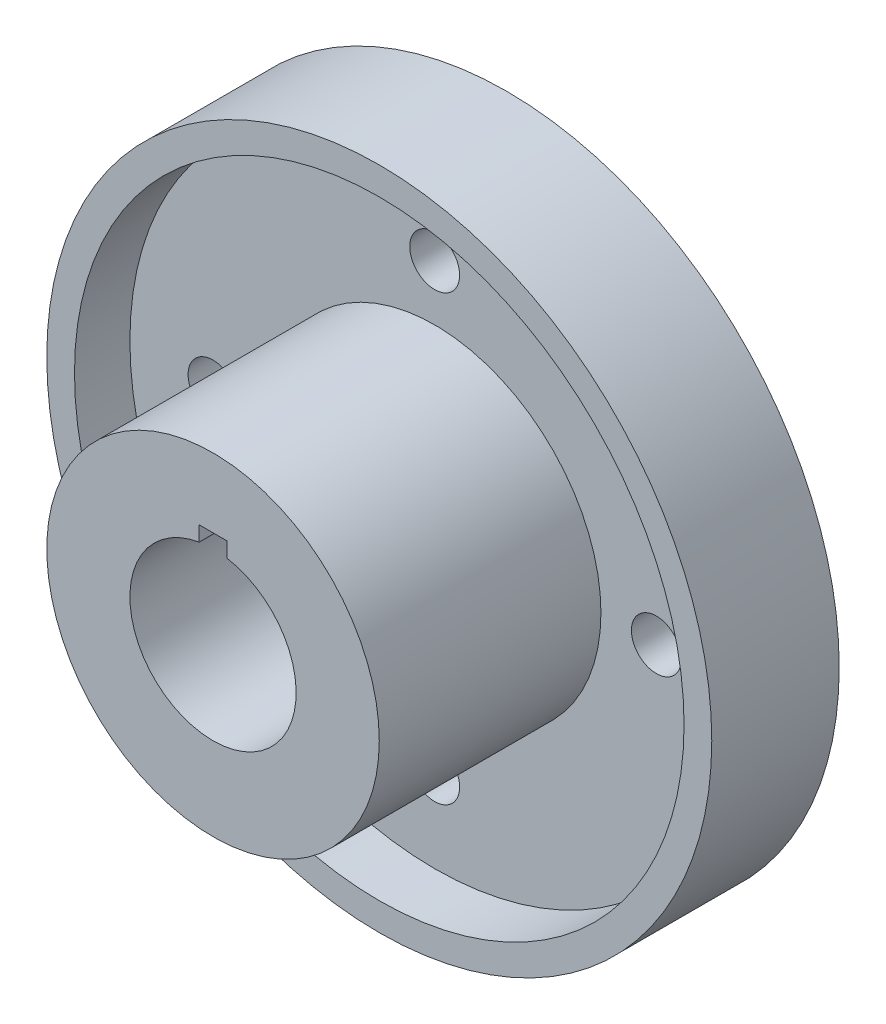
SolidWorks part; units mm, degrees
material "AISI 1020"
ref_plane "Front Plane" through (0, 0, 0) normal (0, 0, 1) x (1, 0, 0)
ref_plane "Top Plane" through (0, 0, 0) normal (0, 1, 0) x (1, 0, 0)
ref_plane "Right Plane" through (0, 0, 0) normal (1, 0, 0) x (0, 0, -1)
sketch "Sketch1" plane through (0, 0, 0) normal (1, 0, 0) x (0, 0, -1)
  line L0 (0, 0) -> (98.4503, 0) construction
  line L1 (-3, 15) -> (-53, 15)
  line L2 (-53, 15) -> (-53, 30)
  line L3 (-53, 30) -> (-13, 30)
  line L4 (-13, 30) -> (-13, 55)
  line L5 (-13, 55) -> (-23, 55)
  line L6 (-23, 55) -> (-23, 60)
  line L7 (-23, 60) -> (0, 60)
  line L9 (0, 60) -> (0, 55)
  line L10 (0, 55) -> (-3, 55)
  line L11 (-3, 55) -> (-3, 33.8855)
  line L12 (-3, 33.8855) -> (-3, 15)
  dimension "D1" = 30
  dimension "D2" = 60
  dimension "D3" = 110
  dimension "D4" = 120
  dimension "D5" = 3
  dimension "D6" = 13
  dimension "D7" = 23
  dimension "D8" = 53
revolve "Revolve1" add sketch "Sketch1" angle 360 about L0
sketch "Sketch2" plane through (0, 0, 53) normal (0, 0, 1) x (1, 0, 0)
  line L1 (-2.5, 12.5) -> (2.5, 12.5)
  line L2 (-2.5, 12.5) -> (-2.5, 17.5)
  line L3 (-2.5, 17.5) -> (2.5, 17.5)
  line L4 (2.5, 12.5) -> (2.5, 17.5)
  dimension "D1" = 5
  dimension "D2" = 5
  dimension "D3" = 12.5
  dimension "D4" = 2.5
extrude "Cut-Extrude1" cut sketch "Sketch2" against normal through all
hole_wizard "M8 Clearance Hole2" positions "Sketch7" profile "Sketch8" hole size "M8" standard "ANSI Metric" end condition through all
sketch "Sketch7" plane through (0, 0, 13) normal (0, 0, 1) x (1, 0, 0)
  point P0 (0, 40)
  dimension "D1" = 40
sketch "Sketch8" plane through (0, 40, 13) normal (1, 0, 0) x (0, -1, 0)
  line L0 (0, 0) -> (0, 13)
  line L1 (0, 13) -> (4.5, 13)
  line L2 (4.5, 13) -> (4.5, 0)
  line L5 (4.5, 0) -> (0, 0)
  line L11 (0, -6.35) -> (0, 107.95) construction
  dimension "Thru Hole Dia." = 9
  dimension "Thru Hole Depth" = 13
pattern_circular "CirPattern1" count 4 over 360 about axis through (0, 0, 0) along (0, 0, 1) of "M8 Clearance Hole2"
